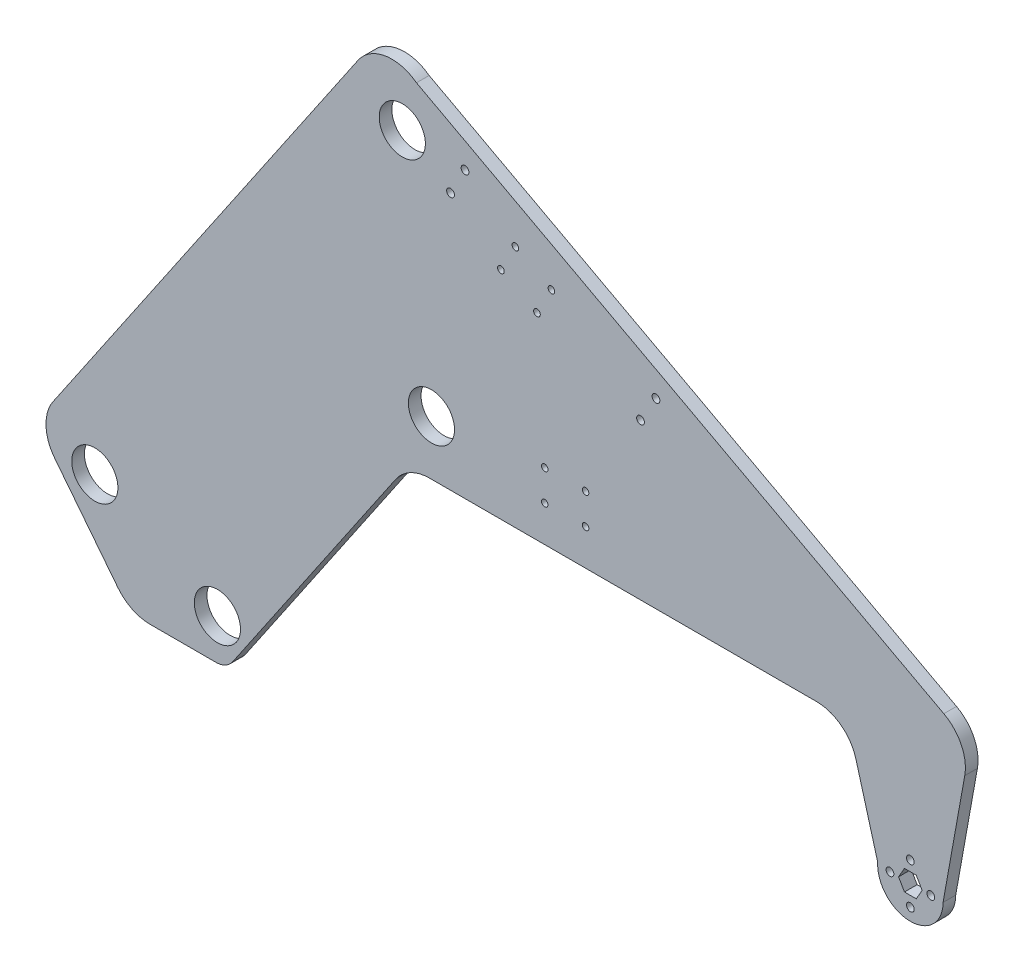
SolidWorks part; units mm, degrees
other "Markup1"
sketch "Sketch1" plane through (-441.7893, 331.8239, 6.35) normal (-0.0431, 0.0102, 0.999) x (0.9985, 0.0354, 0.0427)
sketch "Sketch2" plane through (-413.6701, 343.933, 6.35) normal (-0.0431, 0.0102, 0.999) x (0.9985, 0.0354, 0.0427)
sketch "Sketch3" plane through (-436.3774, 318.5567, 6.35) normal (-0.0431, 0.0102, 0.999) x (0.9985, 0.0354, 0.0427)
sketch "Sketch5" plane through (-436.3774, 318.5567, 6.35) normal (-0.0431, 0.0102, 0.999) x (0.9985, 0.0354, 0.0427)
sketch "Sketch7" plane through (-430.3226, 318.5567, 6.35) normal (-0.0431, 0.0102, 0.999) x (0.9985, 0.0354, 0.0427)
sketch "Sketch9" plane through (-430.3226, 318.5567, 6.35) normal (-0.0431, 0.0102, 0.999) x (0.9985, 0.0354, 0.0427)
sketch "Sketch11" plane through (-430.3226, 318.5567, 6.35) normal (-0.0431, 0.0102, 0.999) x (0.9985, 0.0354, 0.0427)
sketch "Sketch13" plane through (-430.3226, 318.5567, 6.35) normal (-0.0431, 0.0102, 0.999) x (0.9985, 0.0354, 0.0427)
sketch "Sketch15" plane through (-430.3271, 318.5486, 7.874) normal (-0.0431, 0.0102, 0.999) x (0.9985, 0.0354, 0.0427)
sketch "Sketch19" plane through (-430.3271, 318.5486, 7.874) normal (-0.0431, 0.0102, 0.999) x (0.9985, 0.0354, 0.0427)
sketch "Sketch21" plane through (-430.3271, 318.5486, 7.874) normal (-0.0431, 0.0102, 0.999) x (0.9985, 0.0354, 0.0427)
sketch "Sketch23" plane through (-430.3271, 318.5486, 7.874) normal (-0.0431, 0.0102, 0.999) x (0.9985, 0.0354, 0.0427)
other "Markup2"
sketch "Sketch4" plane through (102.4721, 318.5567, 6.35) normal (0.9364, 0.1073, 0.3342) x (0.3416, -0.0598, -0.9379)
sketch "Sketch6" plane through (102.4721, 318.5567, 6.35) normal (0.9364, 0.1073, 0.3342) x (0.3416, -0.0598, -0.9379)
sketch "Sketch8" plane through (141.2086, 318.5567, 6.35) normal (0.9364, 0.1073, 0.3342) x (0.3416, -0.0598, -0.9379)
sketch "Sketch10" plane through (141.2086, 318.5567, 6.35) normal (0.9364, 0.1073, 0.3342) x (0.3416, -0.0598, -0.9379)
sketch "Sketch12" plane through (141.2086, 318.5567, 6.35) normal (0.9364, 0.1073, 0.3342) x (0.3416, -0.0598, -0.9379)
sketch "Sketch14" plane through (141.2086, 318.5567, 6.35) normal (0.9364, 0.1073, 0.3342) x (0.3416, -0.0598, -0.9379)
sketch "Sketch16" plane through (141.2086, 318.5486, 7.874) normal (0.9364, 0.1073, 0.3342) x (0.3416, -0.0598, -0.9379)
sketch "Sketch20" plane through (141.2086, 318.5486, 7.874) normal (0.9364, 0.1073, 0.3342) x (0.3416, -0.0598, -0.9379)
sketch "Sketch22" plane through (141.2086, 318.5486, 7.874) normal (0.9364, 0.1073, 0.3342) x (0.3416, -0.0598, -0.9379)
sketch "Sketch24" plane through (141.2086, 318.5486, 7.874) normal (0.9364, 0.1073, 0.3342) x (0.3416, -0.0598, -0.9379)
material "Lexan"
ref_plane "Front Plane" through (0, 0, 0) normal (0, 0, 1) x (1, 0, 0)
ref_plane "Top Plane" through (0, 0, 0) normal (0, 1, 0) x (1, 0, 0)
ref_plane "Right Plane" through (0, 0, 0) normal (1, 0, 0) x (0, 0, -1)
sketch "Model" plane through (0, 0, 0) normal (0, 0, 1) x (1, 0, 0)
  line L1 (-191.9011, 104.6502) -> (-112.96, 104.6502)
  line L3 (-314.2383, -55.3595) -> (-212.8994, 93.5413)
  line L4 (-236.3088, 307.4396) -> (-425.9253, 28.8296)
  line L5 (-424.901, -1.1522) -> (-385.5815, -51.2048)
  line L13 (114.3386, 35.8116) -> (110.6724, 42.1616)
  line L14 (110.6724, 42.1616) -> (103.3401, 42.1616)
  line L15 (103.3401, 42.1616) -> (99.6739, 35.8116)
  line L16 (99.6739, 35.8116) -> (103.3401, 29.4616)
  line L17 (103.3401, 29.4616) -> (110.6724, 29.4616)
  line L18 (110.6724, 29.4616) -> (114.3386, 35.8116)
  line L19 (-365.6075, -60.914) -> (-324.7375, -60.914)
  line L20 (-871.0211, -88.854) -> (370.1019, -88.854) construction
  line L22 (127.3262, 35.8116) -> (140.8079, 110.8095)
  line L28 (-399.9752, 2.586) -> (-323.7752, -35.514) construction
  line L29 (-323.7752, -35.514) -> (-190.7071, 138.5169) construction
  line L30 (-190.7071, 138.5169) -> (-208.8329, 283.4378) construction
  line L31 (-208.8329, 283.4378) -> (-399.9752, 2.586) construction
  line L32 (86.727, 37.0982) -> (73.1352, 86.0462)
  line L33 (48.6612, 104.6502) -> (-11.3966, 104.6502)
  line L34 (107.0062, 42.1616) -> (107.0062, 48.5116)
  line L35 (127.8091, 137.6897) -> (-86.3327, 252.4836)
  line L40 (-68.51, 104.6502) -> (-2.1388, 104.6502)
  line L41 (-122.3008, 271.7648) -> (-200.0053, 313.4195)
  line L42 (-122.3008, 271.7648) -> (-86.3327, 252.4836)
  line L43 (-112.96, 104.6502) -> (-68.51, 104.6502)
  line L50 (-200.0053, 313.4195) -> (-49.9227, 219.9967)
  line L51 (-49.9227, 219.9967) -> (-44.5225, 230.0706)
  line L52 (-52.2617, 215.9867) -> (-49.9227, 219.9967)
  line L53 (-200.0053, 313.4195) -> (-168.7063, 283.6725)
  line L54 (-168.7063, 283.6725) -> (-163.306, 293.7463)
  line L55 (-168.7063, 283.6725) -> (-170.9864, 279.419)
  line L56 (-169.8463, 281.5458) -> (-170.9864, 279.419) construction
  arc A3 (86.727, 37.0982) -> (127.3262, 35.8116) centre (107.0062, 35.8116) ccw
  circle A9 centre (-323.7752, -35.514) radius 14.351
  circle A10 centre (-399.9752, 2.586) radius 14.351
  circle A12 centre (-190.7071, 138.5169) radius 14.351
  arc A21 (-191.9011, 104.6502) -> (-212.8994, 93.5413) centre (-191.9011, 79.2502) ccw
  circle A22 centre (-208.8329, 283.4378) radius 14.351
  circle A24 centre (107.0062, 35.8116) radius 6.35 construction
  arc A31 (-324.7375, -60.914) -> (-314.2383, -55.3595) centre (-324.7375, -48.214) ccw
  arc A40 (100.8518, 33.7713) -> (100.8849, 34.1227) centre (81.9032, 35.734) ccw
  arc A44 (-236.3088, 307.4396) -> (-200.0053, 313.4195) centre (-215.3105, 293.1486) cw
  arc A45 (-365.6075, -60.914) -> (-385.5815, -51.2048) centre (-365.6075, -35.514) cw
  arc A46 (73.1352, 86.0462) -> (48.6612, 104.6502) centre (48.6612, 79.2502) ccw
  arc A47 (140.8079, 110.8095) -> (127.8091, 137.6897) centre (115.8086, 115.3033) ccw
  arc A48 (-424.901, -1.1522) -> (-425.9253, 28.8296) centre (-404.9271, 14.5386) cw
  circle A57 centre (-51.1385, 217.9124) radius 2.413
  circle A61 centre (-60.7368, 201.4572) radius 2.413
  circle A62 centre (-169.8463, 281.5458) radius 2.413
  circle A64 centre (-178.8467, 264.756) radius 2.413
  circle A74 centre (-174.3465, 273.1509) radius 2.413 [skipped]
  circle A75 centre (-55.9377, 209.6848) radius 2.413 [skipped]
  circle A79 centre (107.0062, 48.5116) radius 2.413
  circle A80 centre (119.7062, 35.8116) radius 2.413
  circle A81 centre (107.0062, 23.1116) radius 2.413
  circle A82 centre (94.3062, 35.8116) radius 2.413
  ellipse E0 centre (-551.1692, 173.9527) end of major axis (-591.2054, 216.0961) minor radius 17.278
  point P31 (-177.5612, 328.1601)
  point P34 (100.2935, -12.8222)
  point P43 (-377.9543, -60.914)
  point P55 (96.7586, 34.8002)
  point P59 (167.8774, 35.8116)
  point P60 (-205.3388, 104.6502)
  point P64 (-436.3829, 13.4639)
  point P73 (107.0062, 35.8116)
  point P75 (107.0062, 35.8116)
  point P105 (-150.6354, 228.9492)
  point P118 (-137.5, 129.276)
  dimension "D3" = 38.1
  dimension "D5" = 76.2
  dimension "D6" = 40.64
  dimension "D7" = 12.7
  dimension "D8" = 28.702
  dimension "D11" = 139.7
  dimension "D12" = 27.94
  dimension "D21" = 124.238
  dimension "D13" = 12.7
  dimension "D16" = 355.6
  dimension "D23" = 76.2
  dimension "D24" = 4.826
  dimension "D26" = 242.9699
  dimension "D14" = 50.8
  dimension "D20" = 254
  dimension "D29" = 25.4
  dimension "D31" = 25.4
  dimension "D32" = 25.4
  dimension "D33" = 25.4
  dimension "D42" = 19.05
  dimension "D48" = 4.826
  dimension "D52" = 4.826
  dimension "D41" = 19.05
  dimension "D19" = 6.35
  dimension "D9" = 19.05
  dimension "D10" = 146.05
  dimension "D15" = 33.8667
  dimension "D17" = 339.725
  dimension "D18" = 219.075
  dimension "D22" = 25.4
  dimension "D27" = 53.2168
  dimension "D46" = 176.784
  dimension "D47" = 11.43
  dimension "D50" = 43.18
  dimension "D51" = 11.43
  dimension "D49" = 3
  dimension "D53" = 3
extrude "Boss-Extrude1" add sketch "Model" along normal blind 7.874
sketch "Sketch17" plane through (0, 0, 0) normal (0, 0, -1) x (-1, 0, 0)
  circle A0 centre (138.5332, 255.9082) radius 2.0701
  circle A1 centre (147.5196, 239.111) radius 2.0701
  circle A2 centre (125.1233, 227.1291) radius 2.0701
  circle A3 centre (116.1369, 243.9263) radius 2.0701
extrude "Cut-Extrude1" cut sketch "Sketch17" against normal through all
sketch "Sketch18" plane through (0, 0, 0) normal (0, 0, -1) x (-1, 0, 0)
  circle A0 centre (120.2875, 146.0627) radius 2.0193
  circle A1 centre (120.2875, 127.0127) radius 2.0193
  circle A2 centre (94.8875, 127.0127) radius 2.0193
  circle A3 centre (94.8875, 146.0627) radius 2.0193
  dimension "D1" = 4.0386
  dimension "D2" = 4.0386
  dimension "D3" = 4.0386
  dimension "D4" = 4.0386
  dimension "D5" = 25.4
  dimension "D6" = 25.4
  dimension "D7" = 19.05
extrude "Cut-Extrude2" cut sketch "Sketch18" against normal through all
